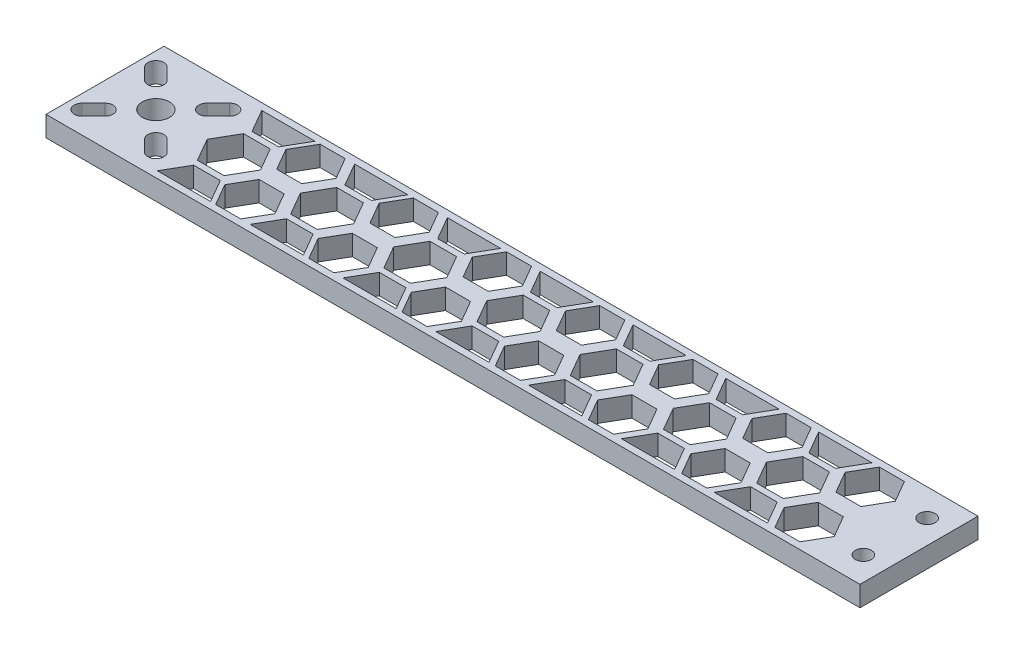
SolidWorks part; units mm, degrees
ref_plane "Front Plane" through (0, 0, 0) normal (0, 0, 1) x (1, 0, 0)
ref_plane "Top Plane" through (0, 0, 0) normal (0, 1, 0) x (1, 0, 0)
ref_plane "Right Plane" through (0, 0, 0) normal (1, 0, 0) x (0, 0, -1)
sketch "Sketch1" plane through (0, 0, 0) normal (0, 1, 0) x (1, 0, 0)
  line L1 (-76.2, 11.049) -> (76.2, 11.049)
  line L2 (-76.2, 11.049) -> (-76.2, -11.049)
  line L3 (-76.2, -11.049) -> (76.2, -11.049)
  line L4 (76.2, 11.049) -> (76.2, -11.049)
  line L5 (-76.2, 11.049) -> (76.2, -11.049) construction
  line L6 (-76.2, -11.049) -> (76.2, 11.049) construction
  circle A0 centre (71.755, 5.969) radius 1.5
  circle A1 centre (71.755, -5.969) radius 1.5
  point P0 (0, 0)
  dimension "D3" = 3
  dimension "D1" = 22.098
  dimension "D2" = 152.4
  dimension "D4" = 4.445
  dimension "D5" = 5.08
  dimension "D6" = 5.08
extrude "Boss-Extrude1" add sketch "Sketch1" along normal blind 3.81
sketch "Sketch2" plane through (0, 3.81, 0) normal (0, 1, 0) x (1, 0, 0)
  line L10 (76.2, 11.049) -> (-76.2, 11.049) construction
  line L11 (-76.2, -11.049) -> (76.2, -11.049) construction
  line L12 (63.6936, -9.779) -> (66.04, -5.715)
  line L13 (66.04, -5.715) -> (63.6936, -1.651)
  line L14 (63.6936, -1.651) -> (59.0009, -1.651)
  line L15 (59.0009, -1.651) -> (56.6546, -5.715)
  line L16 (56.6546, -5.715) -> (59.0009, -9.779)
  line L17 (59.0009, -9.779) -> (63.6936, -9.779)
  line L18 (63.6936, 1.651) -> (66.04, 5.715)
  line L19 (66.04, 5.715) -> (63.6936, 9.779)
  line L20 (63.6936, 9.779) -> (59.0009, 9.779)
  line L21 (59.0009, 9.779) -> (56.6546, 5.715)
  line L22 (56.6546, 5.715) -> (59.0009, 1.651)
  line L23 (59.0009, 1.651) -> (63.6936, 1.651)
  line L24 (76.2, -11.049) -> (76.2, 11.049) construction
  line L26 (46.2427, -9.779) -> (48.589, -5.715)
  line L27 (48.589, -5.715) -> (46.2427, -1.651)
  line L28 (46.2427, -1.651) -> (41.55, -1.651)
  line L29 (41.55, -1.651) -> (39.2036, -5.715)
  line L30 (39.2036, -5.715) -> (41.55, -9.779)
  line L31 (41.55, -9.779) -> (46.2427, -9.779)
  line L32 (46.2427, 1.651) -> (48.589, 5.715)
  line L33 (48.589, 5.715) -> (46.2427, 9.779)
  line L34 (46.2427, 9.779) -> (41.55, 9.779)
  line L35 (41.55, 9.779) -> (39.2036, 5.715)
  line L36 (39.2036, 5.715) -> (41.55, 1.651)
  line L37 (41.55, 1.651) -> (46.2427, 1.651)
  line L38 (37.6638, -4.318) -> (40.1568, 0)
  line L39 (55.1148, -4.318) -> (57.6078, 0)
  line L40 (57.6078, 0) -> (55.1148, 4.318)
  line L41 (55.1148, 4.318) -> (50.1288, 4.318)
  line L42 (50.1288, 4.318) -> (47.6358, 0)
  line L43 (47.6358, 0) -> (50.1288, -4.318)
  line L44 (50.1288, -4.318) -> (55.1148, -4.318)
  line L45 (40.1568, 0) -> (37.6638, 4.318)
  line L46 (37.6638, 4.318) -> (32.6778, 4.318)
  line L47 (32.6778, 4.318) -> (30.1848, 0)
  line L48 (30.1848, 0) -> (32.6778, -4.318)
  line L49 (32.6778, -4.318) -> (37.6638, -4.318)
  line L50 (28.7917, -9.779) -> (31.138, -5.715)
  line L51 (31.138, -5.715) -> (28.7917, -1.651)
  line L52 (28.7917, -1.651) -> (24.099, -1.651)
  line L53 (24.099, -1.651) -> (21.7526, -5.715)
  line L54 (21.7526, -5.715) -> (24.099, -9.779)
  line L55 (24.099, -9.779) -> (28.7917, -9.779)
  line L56 (28.7917, 1.651) -> (31.138, 5.715)
  line L57 (31.138, 5.715) -> (28.7917, 9.779)
  line L58 (28.7917, 9.779) -> (24.099, 9.779)
  line L59 (24.099, 9.779) -> (21.7526, 5.715)
  line L60 (21.7526, 5.715) -> (24.099, 1.651)
  line L61 (24.099, 1.651) -> (28.7917, 1.651)
  line L62 (20.2128, -4.318) -> (22.7058, 0)
  line L63 (22.7058, 0) -> (20.2128, 4.318)
  line L64 (20.2128, 4.318) -> (15.2268, 4.318)
  line L65 (15.2268, 4.318) -> (12.7338, 0)
  line L66 (12.7338, 0) -> (15.2268, -4.318)
  line L67 (15.2268, -4.318) -> (20.2128, -4.318)
  line L68 (11.3407, -9.779) -> (13.687, -5.715)
  line L69 (13.687, -5.715) -> (11.3407, -1.651)
  line L70 (11.3407, -1.651) -> (6.648, -1.651)
  line L71 (6.648, -1.651) -> (4.3016, -5.715)
  line L72 (4.3016, -5.715) -> (6.648, -9.779)
  line L73 (6.648, -9.779) -> (11.3407, -9.779)
  line L74 (11.3407, 1.651) -> (13.687, 5.715)
  line L75 (13.687, 5.715) -> (11.3407, 9.779)
  line L76 (11.3407, 9.779) -> (6.648, 9.779)
  line L77 (6.648, 9.779) -> (4.3016, 5.715)
  line L78 (4.3016, 5.715) -> (6.648, 1.651)
  line L79 (6.648, 1.651) -> (11.3407, 1.651)
  line L80 (2.7618, -4.318) -> (5.2548, 0)
  line L81 (5.2548, 0) -> (2.7618, 4.318)
  line L82 (2.7618, 4.318) -> (-2.2242, 4.318)
  line L83 (-2.2242, 4.318) -> (-4.7172, 0)
  line L84 (-4.7172, 0) -> (-2.2242, -4.318)
  line L85 (-2.2242, -4.318) -> (2.7618, -4.318)
  line L86 (-6.1103, -9.779) -> (-3.764, -5.715)
  line L87 (-3.764, -5.715) -> (-6.1103, -1.651)
  line L88 (-6.1103, -1.651) -> (-10.803, -1.651)
  line L89 (-10.803, -1.651) -> (-13.1494, -5.715)
  line L90 (-13.1494, -5.715) -> (-10.803, -9.779)
  line L91 (-10.803, -9.779) -> (-6.1103, -9.779)
  line L92 (-6.1103, 1.651) -> (-3.764, 5.715)
  line L93 (-3.764, 5.715) -> (-6.1103, 9.779)
  line L94 (-6.1103, 9.779) -> (-10.803, 9.779)
  line L95 (-10.803, 9.779) -> (-13.1494, 5.715)
  line L96 (-13.1494, 5.715) -> (-10.803, 1.651)
  line L97 (-10.803, 1.651) -> (-6.1103, 1.651)
  line L98 (-14.6892, -4.318) -> (-12.1962, 0)
  line L99 (-12.1962, 0) -> (-14.6892, 4.318)
  line L100 (-14.6892, 4.318) -> (-19.6752, 4.318)
  line L101 (-19.6752, 4.318) -> (-22.1682, 0)
  line L102 (-22.1682, 0) -> (-19.6752, -4.318)
  line L103 (-19.6752, -4.318) -> (-14.6892, -4.318)
  line L104 (-23.5613, -9.779) -> (-21.2149, -5.715)
  line L105 (-21.2149, -5.715) -> (-23.5613, -1.651)
  line L106 (-23.5613, -1.651) -> (-28.254, -1.651)
  line L107 (-28.254, -1.651) -> (-30.6004, -5.715)
  line L108 (-30.6004, -5.715) -> (-28.254, -9.779)
  line L109 (-28.254, -9.779) -> (-23.5613, -9.779)
  line L110 (-23.5613, 1.651) -> (-21.2149, 5.715)
  line L111 (-21.2149, 5.715) -> (-23.5613, 9.779)
  line L112 (-23.5613, 9.779) -> (-28.254, 9.779)
  line L113 (-28.254, 9.779) -> (-30.6004, 5.715)
  line L114 (-30.6004, 5.715) -> (-28.254, 1.651)
  line L115 (-28.254, 1.651) -> (-23.5613, 1.651)
  line L116 (-32.1401, -4.318) -> (-29.6471, 0)
  line L117 (-29.6471, 0) -> (-32.1401, 4.318)
  line L118 (-32.1401, 4.318) -> (-37.1261, 4.318)
  line L119 (-37.1261, 4.318) -> (-39.6191, 0)
  line L120 (-39.6191, 0) -> (-37.1261, -4.318)
  line L121 (-37.1261, -4.318) -> (-32.1401, -4.318)
  line L122 (-41.0123, -9.779) -> (-38.6659, -5.715)
  line L123 (-38.6659, -5.715) -> (-41.0123, -1.651)
  line L124 (-41.0123, -1.651) -> (-45.705, -1.651)
  line L125 (-45.705, -1.651) -> (-48.0513, -5.715)
  line L126 (-48.0513, -5.715) -> (-45.705, -9.779)
  line L127 (-45.705, -9.779) -> (-41.0123, -9.779)
  line L128 (-41.0123, 1.651) -> (-38.6659, 5.715)
  line L129 (-38.6659, 5.715) -> (-41.0123, 9.779)
  line L130 (-41.0123, 9.779) -> (-45.705, 9.779)
  line L131 (-45.705, 9.779) -> (-48.0513, 5.715)
  line L132 (-48.0513, 5.715) -> (-45.705, 1.651)
  line L133 (-45.705, 1.651) -> (-41.0123, 1.651)
  line L134 (-49.5911, -4.318) -> (-47.0981, 0)
  line L135 (-47.0981, 0) -> (-49.5911, 4.318)
  line L136 (-49.5911, 4.318) -> (-54.5771, 4.318)
  line L137 (-54.5771, 4.318) -> (-57.0701, 0)
  line L138 (-57.0701, 0) -> (-54.5771, -4.318)
  line L139 (-54.5771, -4.318) -> (-49.5911, -4.318)
  line L170 (57.6078, 9.779) -> (47.6358, 9.779)
  line L171 (55.1148, 5.461) -> (57.6078, 9.779)
  line L175 (47.6358, 9.779) -> (50.1288, 5.461)
  line L176 (50.1288, 5.461) -> (55.1148, 5.461)
  line L177 (57.6078, 0) -> (47.6358, 0) construction
  line L178 (55.1148, 14.097) -> (50.1288, 14.097) [skipped]
  line L179 (52.0573, 17.4373) -> (50.8108, 15.2783) [skipped]
  line L180 (57.6078, 9.779) -> (56.3613, 11.938) [skipped]
  line L181 (55.1148, -5.461) -> (57.6078, -9.779)
  line L182 (50.1288, -5.461) -> (55.1148, -5.461)
  line L183 (47.6358, -9.779) -> (50.1288, -5.461)
  line L184 (57.6078, -9.779) -> (47.6358, -9.779)
  line L185 (40.2301, 9.779) -> (30.2581, 9.779)
  line L186 (30.2581, 9.779) -> (32.7511, 5.461)
  line L187 (32.7511, 5.461) -> (37.7371, 5.461)
  line L188 (37.7371, 5.461) -> (40.2301, 9.779)
  line L189 (37.7371, -5.461) -> (40.2301, -9.779)
  line L190 (40.2301, -9.779) -> (30.2581, -9.779)
  line L191 (30.2581, -9.779) -> (32.7511, -5.461)
  line L192 (32.7511, -5.461) -> (37.7371, -5.461)
  line L193 (22.8525, 9.779) -> (12.8805, 9.779)
  line L194 (12.8805, 9.779) -> (15.3735, 5.461)
  line L195 (15.3735, 5.461) -> (20.3595, 5.461)
  line L196 (20.3595, 5.461) -> (22.8525, 9.779)
  line L197 (20.3595, -5.461) -> (22.8525, -9.779)
  line L198 (22.8525, -9.779) -> (12.8805, -9.779)
  line L199 (12.8805, -9.779) -> (15.3735, -5.461)
  line L200 (15.3735, -5.461) -> (20.3595, -5.461)
  line L201 (5.4748, 9.779) -> (-4.4972, 9.779)
  line L202 (-4.4972, 9.779) -> (-2.0042, 5.461)
  line L203 (-2.0042, 5.461) -> (2.9818, 5.461)
  line L204 (2.9818, 5.461) -> (5.4748, 9.779)
  line L205 (2.9818, -5.461) -> (5.4748, -9.779)
  line L206 (5.4748, -9.779) -> (-4.4972, -9.779)
  line L207 (-4.4972, -9.779) -> (-2.0042, -5.461)
  line L208 (-2.0042, -5.461) -> (2.9818, -5.461)
  line L209 (-11.9029, 9.779) -> (-21.8749, 9.779)
  line L210 (-21.8749, 9.779) -> (-19.3819, 5.461)
  line L211 (-19.3819, 5.461) -> (-14.3959, 5.461)
  line L212 (-14.3959, 5.461) -> (-11.9029, 9.779)
  line L213 (-14.3959, -5.461) -> (-11.9029, -9.779)
  line L214 (-11.9029, -9.779) -> (-21.8749, -9.779)
  line L215 (-21.8749, -9.779) -> (-19.3819, -5.461)
  line L216 (-19.3819, -5.461) -> (-14.3959, -5.461)
  line L217 (-29.2805, 9.779) -> (-39.2525, 9.779)
  line L218 (-39.2525, 9.779) -> (-36.7595, 5.461)
  line L219 (-36.7595, 5.461) -> (-31.7735, 5.461)
  line L220 (-31.7735, 5.461) -> (-29.2805, 9.779)
  line L221 (-31.7735, -5.461) -> (-29.2805, -9.779)
  line L222 (-29.2805, -9.779) -> (-39.2525, -9.779)
  line L223 (-39.2525, -9.779) -> (-36.7595, -5.461)
  line L224 (-36.7595, -5.461) -> (-31.7735, -5.461)
  line L225 (-46.6582, 9.779) -> (-56.6302, 9.779)
  line L226 (-56.6302, 9.779) -> (-54.1372, 5.461)
  line L227 (-54.1372, 5.461) -> (-49.1512, 5.461)
  line L228 (-49.1512, 5.461) -> (-46.6582, 9.779)
  line L229 (-49.1512, -5.461) -> (-46.6582, -9.779)
  line L230 (-46.6582, -9.779) -> (-56.6302, -9.779)
  line L231 (-56.6302, -9.779) -> (-54.1372, -5.461)
  line L232 (-54.1372, -5.461) -> (-49.1512, -5.461)
  line L241 (-58.4633, -1.651) -> (-63.156, -1.651) [skipped]
  line L242 (-63.156, -1.651) -> (-65.5023, -5.715) [skipped]
  line L243 (-65.5023, -5.715) -> (-63.156, -9.779) [skipped]
  line L244 (-63.156, -9.779) -> (-58.4633, -9.779) [skipped]
  line L245 (-58.4633, 1.651) -> (-56.1169, 5.715) [skipped]
  line L246 (-56.1169, 5.715) -> (-58.4633, 9.779) [skipped]
  line L247 (-58.4633, 9.779) -> (-63.156, 9.779) [skipped]
  line L248 (-63.156, 9.779) -> (-65.5023, 5.715) [skipped]
  line L249 (-65.5023, 5.715) -> (-63.156, 1.651) [skipped]
  line L250 (-63.156, 1.651) -> (-58.4633, 1.651) [skipped]
  line L251 (-67.0421, -4.318) -> (-64.5491, 0) [skipped]
  line L252 (-64.5491, 0) -> (-67.0421, 4.318) [skipped]
  line L253 (-67.0421, 4.318) -> (-72.0281, 4.318) [skipped]
  line L254 (-72.0281, 4.318) -> (-74.5211, 0) [skipped]
  line L255 (-74.5211, 0) -> (-72.0281, -4.318) [skipped]
  line L256 (-72.0281, -4.318) -> (-67.0421, -4.318) [skipped]
  line L257 (-75.9143, -9.779) -> (-73.5679, -5.715) [skipped]
  line L258 (-73.5679, -5.715) -> (-75.9143, -1.651) [skipped]
  line L259 (-75.9143, -1.651) -> (-80.607, -1.651) [skipped]
  line L260 (-80.607, -1.651) -> (-82.9533, -5.715) [skipped]
  line L261 (-82.9533, -5.715) -> (-80.607, -9.779) [skipped]
  line L262 (-80.607, -9.779) -> (-75.9143, -9.779) [skipped]
  line L263 (-75.9143, 1.651) -> (-73.5679, 5.715) [skipped]
  line L264 (-73.5679, 5.715) -> (-75.9143, 9.779) [skipped]
  line L265 (-75.9143, 9.779) -> (-80.607, 9.779) [skipped]
  line L266 (-80.607, 9.779) -> (-82.9533, 5.715) [skipped]
  line L267 (-82.9533, 5.715) -> (-80.607, 1.651) [skipped]
  line L268 (-80.607, 1.651) -> (-75.9143, 1.651) [skipped]
  line L269 (-64.0359, 9.779) -> (-74.0079, 9.779) [skipped]
  line L270 (-74.0079, 9.779) -> (-71.5149, 5.461) [skipped]
  line L271 (-71.5149, 5.461) -> (-66.5289, 5.461) [skipped]
  line L272 (-66.5289, 5.461) -> (-64.0359, 9.779) [skipped]
  line L273 (-66.5289, -5.461) -> (-64.0359, -9.779) [skipped]
  line L274 (-64.0359, -9.779) -> (-74.0079, -9.779) [skipped]
  line L275 (-74.0079, -9.779) -> (-71.5149, -5.461) [skipped]
  line L276 (-71.5149, -5.461) -> (-66.5289, -5.461) [skipped]
  line L277 (-56.1169, -5.715) -> (-58.4633, -1.651) [skipped]
  line L278 (-58.4633, -9.779) -> (-56.1169, -5.715) [skipped]
  circle A0 centre (61.3473, -5.715) radius 4.064 construction
  circle A1 centre (52.6218, 0) radius 4.318 construction
  arc A2 (48.3038, 9.779) -> (56.9398, 9.779) centre (52.6218, 9.779) ccw construction
  point P170 (40.3768, 3.683)
  point P180 (62.8288, 5.461)
  dimension "D1" = 8.128
  dimension "D6" = 8.636
  dimension "D2" = 1.27
  dimension "D4" = 2.032
  dimension "D5" = 1.27
  dimension "D7" = 2.032
  dimension "D9" = 2.032
  dimension "D10" = 8
  dimension "D11" = 10.16
  dimension "D12" = 2.032
  dimension "D14" = 1.27
  dimension "D3" = 2
  dimension "D8" = 2
  dimension "D13" = 8
extrude "Cut-Extrude1" cut sketch "Sketch2" against normal up to next (3.81 mm away)
sketch "Sketch3" plane through (0, 3.81, 0) normal (0, 1, 0) x (1, 0, 0)
  line L0 (-66.675, 0) -> (-72.9612, -6.2862) construction
  line L1 (-66.675, 0) -> (-72.9612, 6.2862) construction
  line L2 (-66.675, 0) -> (-60.3888, 6.2862) construction
  line L3 (-66.675, 0) -> (-60.3888, -6.2862) construction
  line L4 (-64.135, 0) -> (-69.215, 0) construction
  line L5 (-76.2, 11.049) -> (-76.2, -11.049) construction
  line L6 (-73.5693, -6.8943) -> (-71.448, -4.773) construction
  line L7 (-74.63, -5.8336) -> (-72.5086, -3.7123)
  line L8 (-72.5086, -7.955) -> (-70.3873, -5.8336)
  line L9 (-74.63, 5.8336) -> (-72.5086, 3.7123)
  line L10 (-72.5086, 7.955) -> (-70.3873, 5.8336)
  line L11 (-73.5693, 6.8943) -> (-71.448, 4.773) construction
  line L12 (-60.8414, 7.955) -> (-62.9627, 5.8336)
  line L13 (-58.72, 5.8336) -> (-60.8414, 3.7123)
  line L14 (-59.7807, 6.8943) -> (-61.902, 4.773) construction
  line L15 (-58.72, -5.8336) -> (-60.8414, -3.7123)
  line L16 (-60.8414, -7.955) -> (-62.9627, -5.8336)
  line L17 (-59.7807, -6.8943) -> (-61.902, -4.773) construction
  circle A0 centre (-66.675, 0) radius 2.54
  arc A1 (-74.63, -5.8336) -> (-72.5086, -7.955) centre (-73.5693, -6.8943) ccw
  arc A2 (-70.3873, -5.8336) -> (-72.5086, -3.7123) centre (-71.448, -4.773) ccw
  arc A3 (-72.5086, 7.955) -> (-74.63, 5.8336) centre (-73.5693, 6.8943) ccw
  arc A4 (-72.5086, 3.7123) -> (-70.3873, 5.8336) centre (-71.448, 4.773) ccw
  arc A5 (-58.72, 5.8336) -> (-60.8414, 7.955) centre (-59.7807, 6.8943) ccw
  arc A6 (-62.9627, 5.8336) -> (-60.8414, 3.7123) centre (-61.902, 4.773) ccw
  arc A7 (-60.8414, -7.955) -> (-58.72, -5.8336) centre (-59.7807, -6.8943) ccw
  arc A8 (-60.8414, -3.7123) -> (-62.9627, -5.8336) centre (-61.902, -4.773) ccw
  point P12 (-72.5086, -5.8336)
  point P18 (-79.375, 0)
  point P22 (-72.5086, 5.8336)
  point P29 (-60.8414, 5.8336)
  point P36 (-60.8414, -5.8336)
  point P42 (-66.675, 0)
  dimension "D2" = 5.08
  dimension "D8" = 1.5
  dimension "D1" = 8.89
  dimension "D3" = 45
  dimension "D4" = 45
  dimension "D5" = 9.525
  dimension "D6" = 3
  dimension "D7" = 9.75
  dimension "D9" = 4
extrude "Cut-Extrude2" cut sketch "Sketch3" against normal up to next
